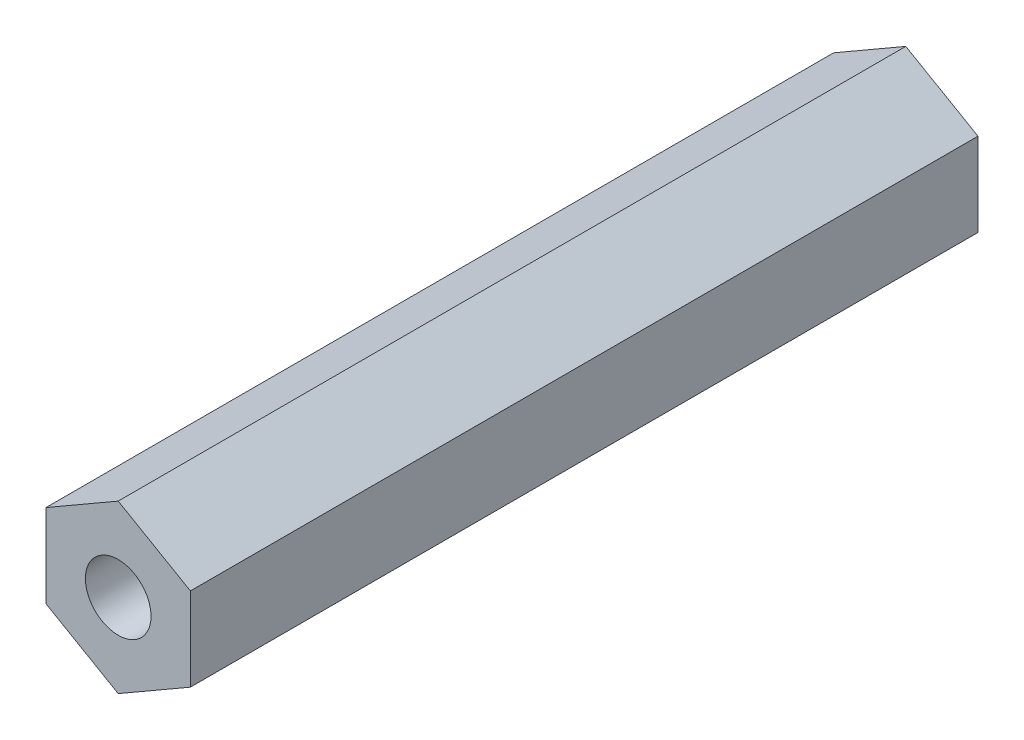
SolidWorks part; units mm, degrees
ref_plane "Plan de face" through (0, 0, 0) normal (0, 0, 1) x (1, 0, 0)
ref_plane "Plan de dessus" through (0, 0, 0) normal (0, 1, 0) x (1, 0, 0)
ref_plane "Plan de droite" through (0, 0, 0) normal (1, 0, 0) x (0, 0, -1)
sketch "Esquisse1" plane through (0, 0, 0) normal (0, 0, 1) x (1, 0, 0)
  line L1 (0, -3.1754) -> (2.75, -1.5877)
  line L2 (2.75, -1.5877) -> (2.75, 1.5877)
  line L3 (2.75, 1.5877) -> (0, 3.1754)
  line L4 (0, 3.1754) -> (-2.75, 1.5877)
  line L5 (-2.75, 1.5877) -> (-2.75, -1.5877)
  line L6 (-2.75, -1.5877) -> (0, -3.1754)
  circle A0 centre (0, 0) radius 2.75 construction
  dimension "D1" = 5.5
extrude "Boss.-Extru.1" add sketch "Esquisse1" along normal blind 30
hole_wizard "Trou pour taraudage pour trou taraudé M31" positions "Esquisse3" profile "Esquisse2" hole size "M3" standard "ISO"
sketch "Esquisse3" plane through (0, 0, 30) normal (0, 0, 1) x (1, 0, 0)
  point P3 (0, 0)
sketch "Esquisse2" plane through (0, 0, 30) normal (1, 0, 0) x (0, -1, 0)
  line L0 (0, 0) -> (0, 7.7511)
  line L1 (0, 7.7511) -> (1.25, 7)
  line L2 (1.25, 7) -> (1.25, 0)
  line L5 (1.25, 0) -> (0, 0)
  line L10 (0, 7.7511) -> (-1.25, 7) construction
  line L11 (0, -6.35) -> (0, 107.95) construction
  dimension "Diamètre du perçage" = 2.5
  dimension "Profondeur du perçage" = 7
  dimension "Angle de pointe" = 118
hole_wizard "Trou pour taraudage pour trou taraudé M32" positions "Esquisse7" profile "Esquisse6" hole size "M3" standard "ISO"
sketch "Esquisse7" plane through (0, 0, 0) normal (0, 0, -1) x (-1, 0, 0)
  point P1 (0, 0)
sketch "Esquisse6" plane through (0, 0, 0) normal (1, 0, 0) x (0, 1, 0)
  line L0 (0, 0) -> (0, 7.7511)
  line L1 (0, 7.7511) -> (1.25, 7)
  line L2 (1.25, 7) -> (1.25, 0)
  line L5 (1.25, 0) -> (0, 0)
  line L10 (0, 7.7511) -> (-1.25, 7) construction
  line L11 (0, -6.35) -> (0, 107.95) construction
  dimension "Diamètre du perçage" = 2.5
  dimension "Profondeur du perçage" = 7
  dimension "Angle de pointe" = 118
